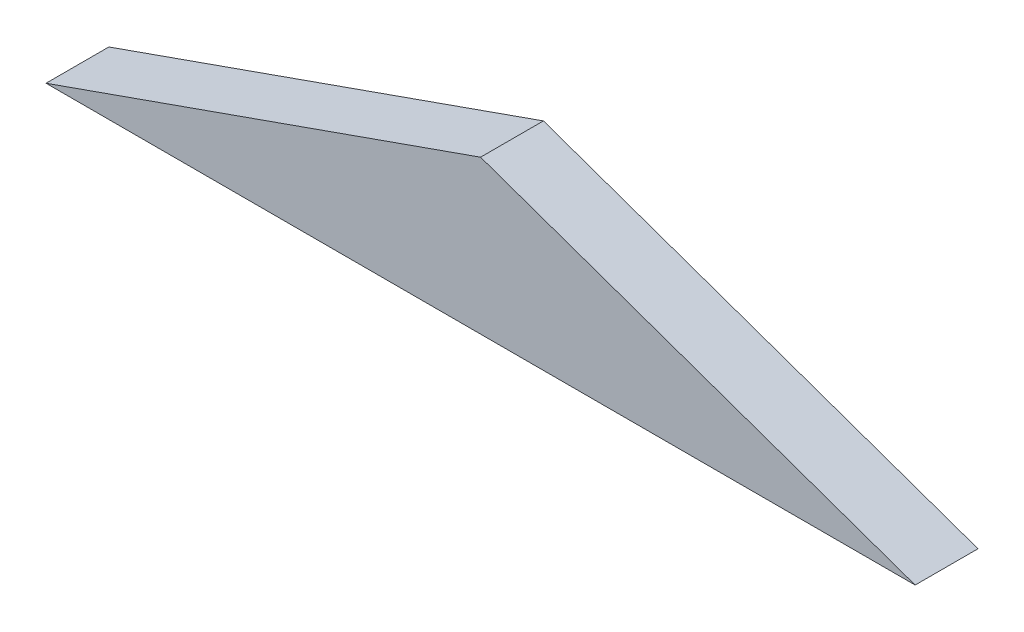
SolidWorks part; units mm, degrees
ref_plane "Plan de face" through (0, 0, 0) normal (0, 0, 1) x (1, 0, 0)
ref_plane "Plan de dessus" through (0, 0, 0) normal (0, 1, 0) x (1, 0, 0)
ref_plane "Plan de droite" through (0, 0, 0) normal (1, 0, 0) x (0, 0, -1)
sketch "Esquisse1" plane through (0, 0, 0) normal (0, 0, 1) x (1, 0, 0)
  line L0 (0, 110) -> (0, 0) construction
  line L1 (0, 110) -> (-20.7478, 102.6836)
  line L2 (-20.7478, 102.6836) -> (20.7478, 102.6836)
  line L3 (0, 110) -> (-160, 53.5782) construction
  line L4 (0, 110) -> (20.7478, 102.6836)
  point P8 (0, 102.6836)
  dimension "D1" = 22
extrude "Boss.-Extru.1" add sketch "Esquisse1" along normal blind 3
